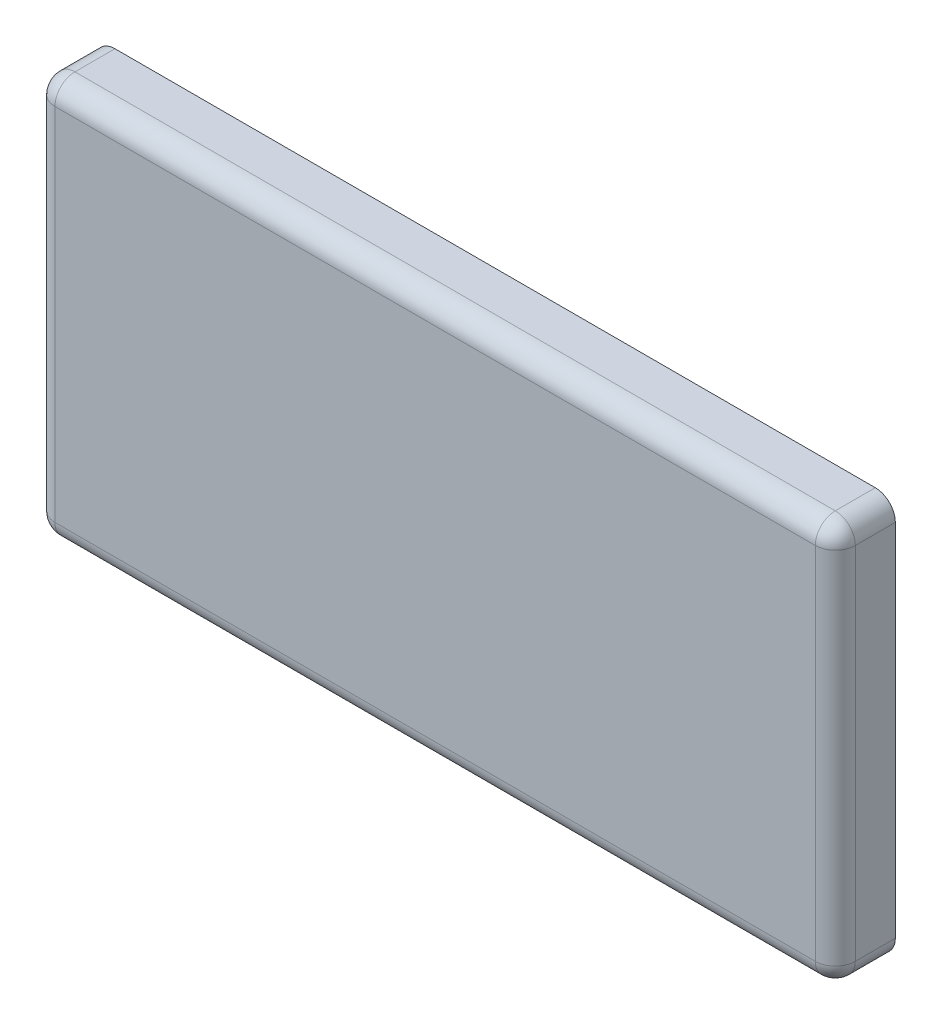
SolidWorks part; units mm, degrees
ref_plane "Front Plane" through (0, 0, 0) normal (0, 0, 1) x (1, 0, 0)
ref_plane "Top Plane" through (0, 0, 0) normal (0, 1, 0) x (1, 0, 0)
ref_plane "Right Plane" through (0, 0, 0) normal (1, 0, 0) x (0, 0, -1)
sketch "Sketch1" plane through (0, 0, 0) normal (0, 0, 1) x (1, 0, 0)
  line L1 (100, -50) -> (-100, -50)
  line L2 (100, -50) -> (100, 50)
  line L3 (100, 50) -> (-100, 50)
  line L4 (-100, -50) -> (-100, 50)
  line L5 (100, -50) -> (-100, 50) construction
  line L6 (100, 50) -> (-100, -50) construction
  point P0 (0, 0)
  dimension "D1" = 100
  dimension "D2" = 200
extrude "Boss-Extrude1" add sketch "Sketch1" along normal blind 15
fillet "Fillet1" radius 5 8 edges at (0, 50, 15) (100, 0, 15) (0, -50, 15) (-100, 0, 15) (-100, 50, 7.5) (100, 50, 7.5) (100, -50, 7.5) (-100, -50, 7.5)
